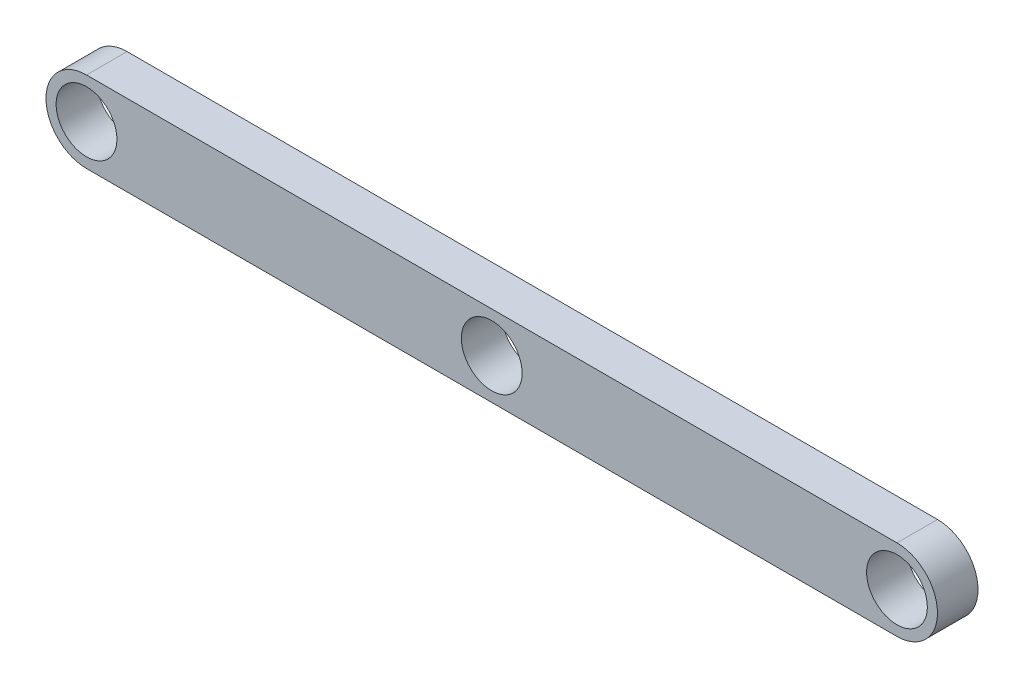
SolidWorks part; units mm, degrees
ref_plane "Front Plane" through (0, 0, 0) normal (0, 0, 1) x (1, 0, 0)
ref_plane "Top Plane" through (0, 0, 0) normal (0, 1, 0) x (1, 0, 0)
ref_plane "Right Plane" through (0, 0, 0) normal (1, 0, 0) x (0, 0, -1)
sketch "Sketch1" plane through (0, 0, 0) normal (0, 0, 1) x (1, 0, 0)
  line L1 (-63.5, -6.35) -> (63.5, -6.35)
  line L3 (-63.5, 6.35) -> (63.5, 6.35)
  line L5 (-63.5, -6.35) -> (63.5, 6.35) construction
  line L6 (-63.5, 6.35) -> (63.5, -6.35) construction
  arc A0 (-63.5, 6.35) -> (-63.5, -6.35) centre (-63.5, 0) ccw
  arc A1 (63.5, -6.35) -> (63.5, 6.35) centre (63.5, 0) ccw
  point P0 (0, 0)
  dimension "D3" = 6.35
  dimension "D4" = 12.7
  dimension "D2" = 6.35
  dimension "D1" = 127
extrude "Boss-Extrude1" add sketch "Sketch1" along normal blind 6.35
sketch "Sketch3" plane through (0, 0, 6.35) normal (0, 0, 1) x (1, 0, 0)
  point P0 (0, 0)
  point P7 (-63.5, 0)
  point P8 (63.5, 0)
  point P9 (0, 0)
  dimension "D1" = 63.5
  dimension "D2" = 63.5
hole_wizard "#4 (0.375) Diameter Hole1" positions "Sketch3" profile "Sketch4" hole size "#4" standard "ANSI Inch" end condition up to next
sketch "Sketch4" plane through (0, 0, 6.35) normal (1, 0, 0) x (0, -1, 0)
  line L0 (0, 0) -> (0, 6.35)
  line L1 (0, 6.35) -> (4.7625, 6.35)
  line L2 (4.7625, 6.35) -> (4.7625, 0)
  line L5 (4.7625, 0) -> (0, 0)
  line L11 (0, -6.35) -> (0, 107.95) construction
  dimension "Thru Hole Dia." = 9.525
  dimension "Thru Hole Depth" = 6.35
